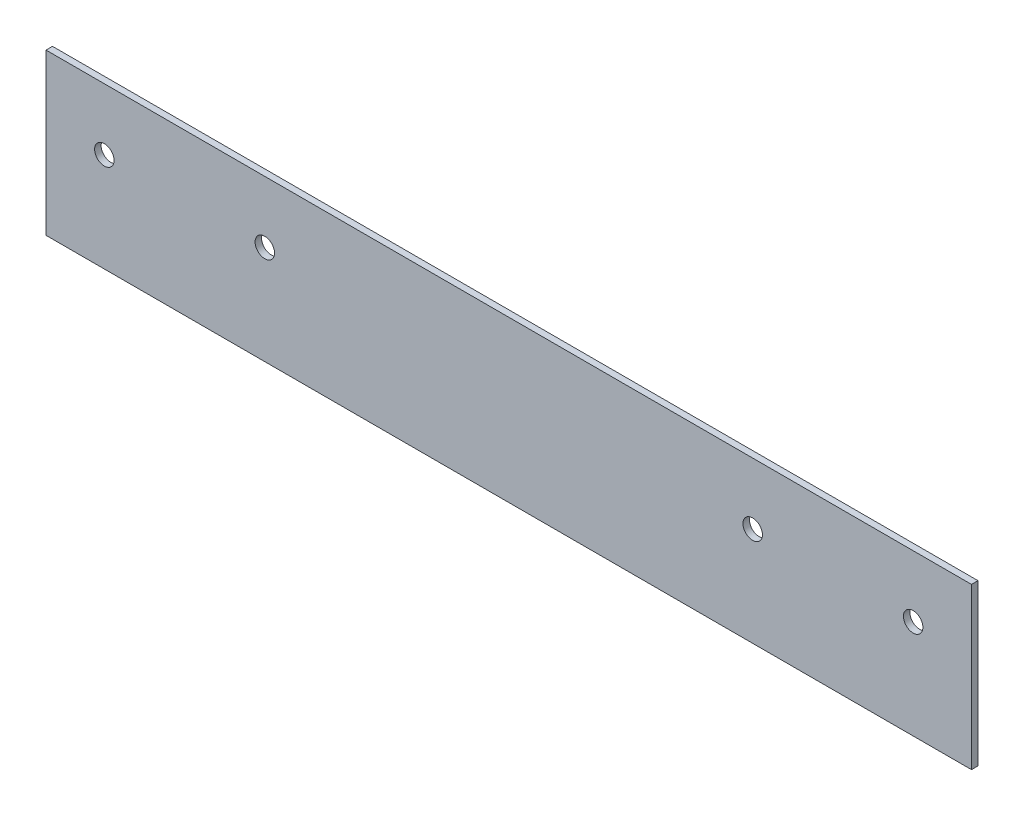
SolidWorks part; units mm, degrees
ref_plane "Front Plane" through (0, 0, 0) normal (0, 0, 1) x (1, 0, 0)
ref_plane "Top Plane" through (0, 0, 0) normal (0, 1, 0) x (1, 0, 0)
ref_plane "Right Plane" through (0, 0, 0) normal (1, 0, 0) x (0, 0, -1)
sketch "Sketch1" plane through (0, 0, 0) normal (0, 0, 1) x (1, 0, 0)
  line L0 (-100, 0) -> (100, 0) construction
  line L1 (100, 30.5) -> (100, -30.5) construction
  line L2 (-100, 30.5) -> (-100, -30.5) construction
  line L3 (0, 65.1273) -> (0, -64.235) construction
  line L4 (-142.75, 49.5) -> (-142.75, 0)
  line L5 (-142.75, 0) -> (0, 0)
  line L9 (-142.75, 49.5) -> (142.75, 49.5)
  line L10 (142.75, 49.5) -> (142.75, 0)
  line L11 (142.75, 0) -> (0, 0)
  circle A0 centre (124.75, 30.5) radius 3
  circle A3 centre (75.25, 30.5) radius 3
  circle A5 centre (-75.25, 30.5) radius 3
  circle A6 centre (-124.75, 30.5) radius 3
  point P3 (0, 0)
  point P44 (-142.75, 0)
  dimension "D3" = 6
  dimension "D1" = 100
  dimension "D5" = 30.5
  dimension "D7" = 285.5
  dimension "D8" = 142.75
  dimension "D9" = 49.5
  dimension "D10" = 49.5
extrude "Boss-Extrude1" add sketch "Sketch1" along normal blind 2
